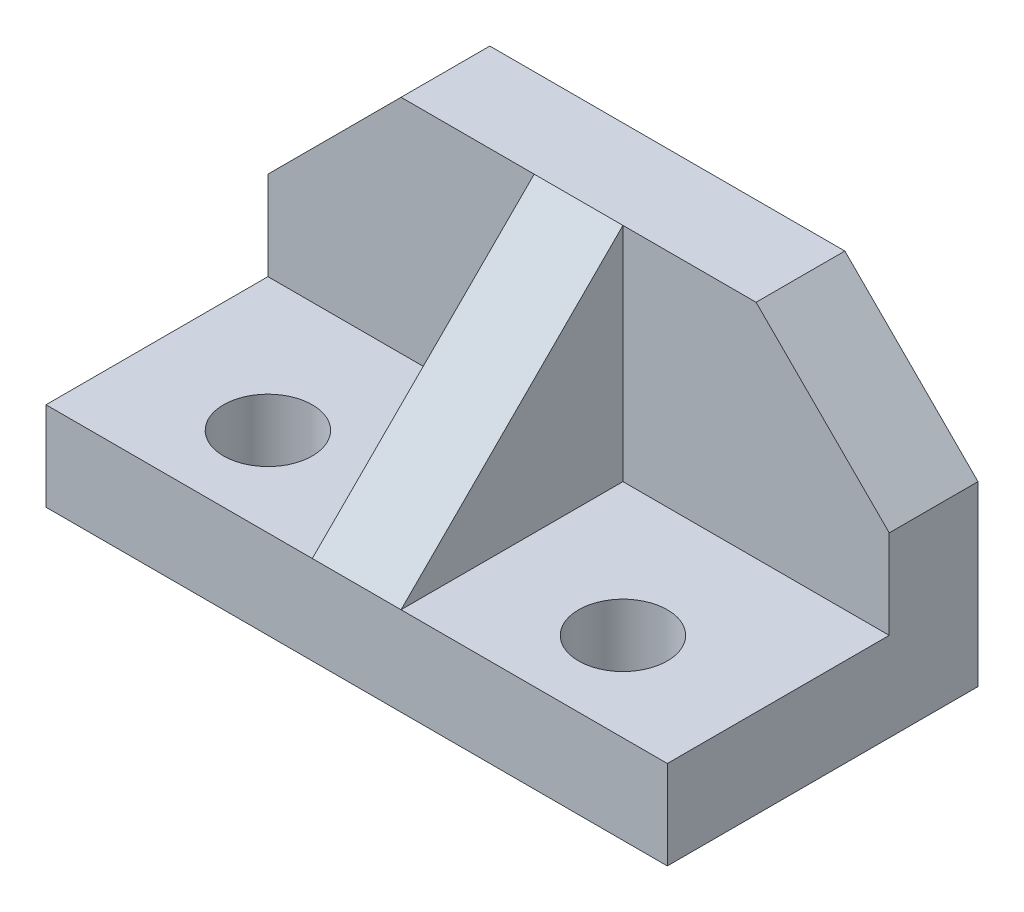
SolidWorks part; units mm, degrees
ref_plane "Front Plane" through (0, 0, 0) normal (0, 0, 1) x (1, 0, 0)
ref_plane "Top Plane" through (0, 0, 0) normal (0, 1, 0) x (1, 0, 0)
ref_plane "Right Plane" through (0, 0, 0) normal (1, 0, 0) x (0, 0, -1)
sketch "Sketch2" plane through (0, 0, 0) normal (0, 1, 0) x (1, 0, 0)
  line L1 (0, 0) -> (70, 0)
  line L2 (0, 0) -> (0, 35)
  line L3 (0, 35) -> (70, 35)
  line L4 (70, 0) -> (70, 35)
  dimension "D1" = 70
  dimension "D2" = 35
extrude "Boss-Extrude1" add sketch "Sketch2" along normal blind 35
sketch "Sketch3" plane through (0, 0, 0) normal (0, 0, 1) x (1, 0, 0)
  line L1 (70, 35) -> (40, 35)
  line L2 (70, 35) -> (70, 10)
  line L3 (70, 10) -> (40, 10)
  line L4 (40, 35) -> (40, 10)
  dimension "D1" = 30
  dimension "D2" = 25
extrude "Cut-Extrude1" cut sketch "Sketch3" against normal blind 25
sketch "Sketch4" plane through (0, 0, 0) normal (0, 0, 1) x (1, 0, 0)
  line L1 (0, 35) -> (30, 35)
  line L2 (0, 35) -> (0, 10)
  line L3 (0, 10) -> (30, 10)
  line L4 (30, 35) -> (30, 10)
  dimension "D1" = 30
  dimension "D2" = 25
extrude "Cut-Extrude2" cut sketch "Sketch4" against normal blind 25
sketch "Sketch5" plane through (40, 0, 0) normal (1, 0, 0) x (0, 0, -1)
  line L0 (0, 10) -> (25, 35)
  line L1 (25, 35) -> (0, 35)
  line L2 (0, 35) -> (0, 10)
extrude "Cut-Extrude3" cut sketch "Sketch5" against normal blind 25
sketch "Sketch6" plane through (0, 0, -25) normal (0, 0, 1) x (1, 0, 0)
  line L0 (70, 35) -> (70, 20)
  line L1 (70, 10) -> (70, 35) construction
  line L2 (70, 20) -> (55, 35)
  line L3 (70, 35) -> (40, 35) construction
  line L4 (55, 35) -> (70, 35)
  dimension "D1" = 15
  dimension "D2" = 15
extrude "Cut-Extrude4" cut sketch "Sketch6" against normal blind 25
sketch "Sketch7" plane through (0, 0, -25) normal (0, 0, 1) x (1, 0, 0)
  line L0 (0, 35) -> (0, 20)
  line L1 (0, 35) -> (0, 10) construction
  line L2 (0, 20) -> (15, 35)
  line L3 (30, 35) -> (0, 35) construction
  line L4 (15, 35) -> (0, 35)
  dimension "D1" = 15
  dimension "D2" = 15
extrude "Cut-Extrude5" cut sketch "Sketch7" against normal blind 25
sketch "Sketch8" plane through (0, 10, 0) normal (0, 1, 0) x (1, 0, 0)
  line L0 (70, 0) -> (55, 0) construction
  line L1 (40, 0) -> (70, 0) construction
  line L2 (55, 0) -> (55, 10) construction
  circle A0 centre (55, 10) radius 5
  dimension "D1" = 10
extrude "Cut-Extrude6" cut sketch "Sketch8" against normal through all
sketch "Sketch9" plane through (0, 10, 0) normal (0, 1, 0) x (1, 0, 0)
  line L0 (0, 0) -> (15, 0) construction
  line L1 (0, 0) -> (30, 0) construction
  line L2 (15, 0) -> (15, 10) construction
  circle A0 centre (15, 10) radius 5
  dimension "D1" = 10
extrude "Cut-Extrude7" cut sketch "Sketch9" against normal through all
